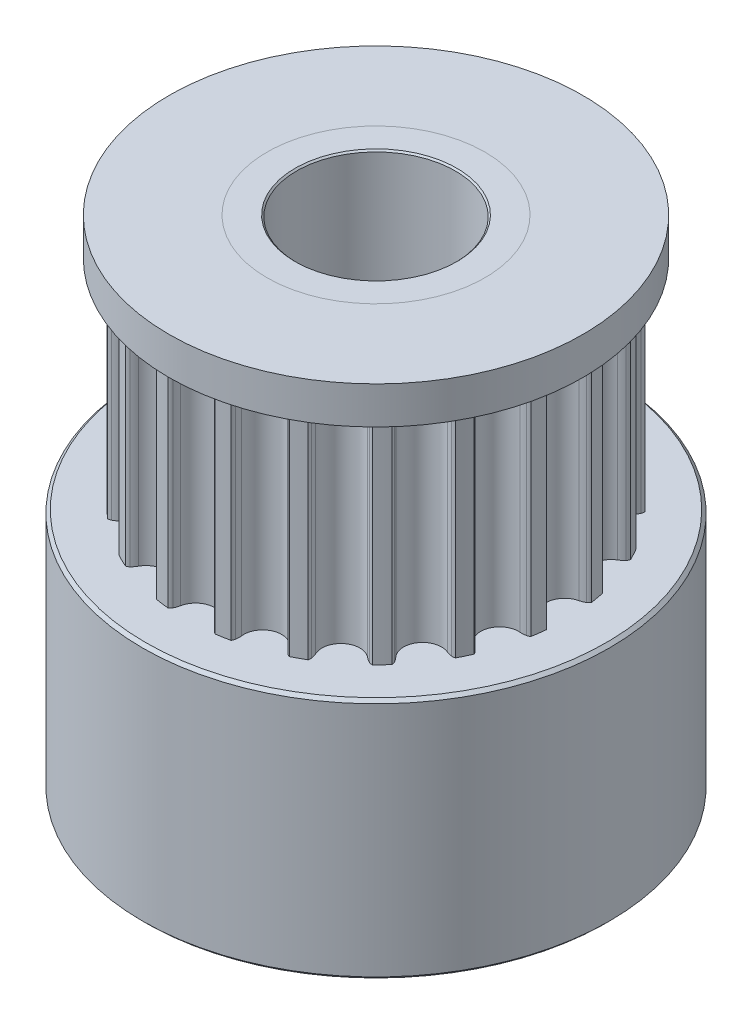
SolidWorks part; units mm, degrees
material "6061 slitina"
ref_plane "Přední rovina" through (0, 0, 0) normal (0, 0, 1) x (1, 0, 0)
ref_plane "Horní rovina" through (0, 0, 0) normal (0, 1, 0) x (1, 0, 0)
ref_plane "Pravá rovina" through (0, 0, 0) normal (1, 0, 0) x (0, 0, -1)
sketch "Skica1" plane through (0, 0, 0) normal (0, 1, 0) x (1, 0, 0)
  circle A0 centre (0, 0) radius 2.5
  arc B0 (-5.7301, 1.0983) -> (-5.3872, 2.2403) centre (-5.6803, 1.7058) ccw
  arc B1 (-5.7301, 1.0983) -> (-5.922, 1.0859) centre (-5.7841, 0.4401) ccw
  arc B2 (-5.922, 1.0859) -> (-6.0197, 1.0387) centre (-5.8743, 0.8624) ccw
  arc B3 (-6.0197, 1.0387) -> (-6.0791, 0.6004) centre (0, 0) ccw
  arc B4 (-6.0791, 0.6004) -> (-5.9974, 0.5289) centre (-5.892, 0.7317) ccw
  arc B5 (-5.9974, 0.5289) -> (-5.8158, 0.466) centre (-5.6927, 1.1148) ccw
  arc B6 (-5.7891, -0.7262) -> (-5.8158, 0.466) centre (-5.9294, -0.133) ccw
  arc B7 (-5.7891, -0.7262) -> (-5.9677, -0.7972) centre (-5.637, -1.3689) ccw
  arc B8 (-5.9677, -0.7972) -> (-6.0461, -0.8723) centre (-5.8532, -0.9951) ccw
  arc B9 (-6.0461, -0.8723) -> (-5.9671, -1.3075) centre (0, 0) ccw
  arc B10 (-5.9671, -1.3075) -> (-5.8673, -1.3503) centre (-5.8297, -1.1248) ccw
  arc B11 (-5.8673, -1.3503) -> (-5.6751, -1.354) centre (-5.7586, -0.6989) ccw
  arc B12 (-5.2813, -2.4796) -> (-5.6751, -1.354) centre (-5.5981, -1.9587) ccw
  arc B13 (-5.2813, -2.4796) -> (-5.4293, -2.6023) centre (-4.9381, -3.0438) ccw
  arc B14 (-5.4293, -2.6023) -> (-5.4806, -2.698) centre (-5.2593, -2.7551) ccw
  arc B15 (-5.4806, -2.698) -> (-5.271, -3.0875) centre (0, 0) ccw
  arc B16 (-5.271, -3.0875) -> (-5.1629, -3.0973) centre (-5.1968, -2.8713) ccw
  arc B17 (-5.1629, -3.0973) -> (-4.979, -3.0415) centre (-5.2608, -2.4442) ccw
  arc B18 (-4.2566, -3.9902) -> (-4.979, -3.0415) centre (-4.7188, -3.5928) ccw
  arc B19 (-4.2566, -3.9902) -> (-4.3594, -4.1527) centre (-3.7559, -4.4208) ccw
  arc B20 (-4.3594, -4.1527) -> (-4.3786, -4.2595) centre (-4.1505, -4.2455) ccw
  arc B21 (-4.3786, -4.2595) -> (-4.059, -4.5652) centre (0, 0) ccw
  arc B22 (-4.059, -4.5652) -> (-3.9531, -4.5412) centre (-4.0552, -4.3366) ccw
  arc B23 (-3.9531, -4.5412) -> (-3.7954, -4.4312) centre (-4.248, -3.9503) ccw
  arc B24 (-2.8152, -5.1103) -> (-3.7954, -4.4312) centre (-3.3776, -4.8751) ccw
  arc B25 (-2.8152, -5.1103) -> (-2.8628, -5.2965) centre (-2.2059, -5.3651) ccw
  arc B26 (-2.8628, -5.2965) -> (-2.8481, -5.4041) centre (-2.6354, -5.3203) ccw
  arc B27 (-2.8481, -5.4041) -> (-2.4496, -5.596) centre (0, 0) ccw
  arc B28 (-2.4496, -5.596) -> (-2.3563, -5.5405) centre (-2.5166, -5.3775) ccw
  arc B29 (-2.3563, -5.5405) -> (-2.2403, -5.3872) centre (-2.8194, -5.0696) ccw
  arc B30 (-1.0983, -5.7301) -> (-2.2403, -5.3872) centre (-1.7058, -5.6803) ccw
  arc B31 (-1.0983, -5.7301) -> (-1.0859, -5.922) centre (-0.4401, -5.7841) ccw
  arc B32 (-1.0859, -5.922) -> (-1.0387, -6.0197) centre (-0.8624, -5.8743) ccw
  arc B33 (-1.0387, -6.0197) -> (-0.6004, -6.0791) centre (0, 0) ccw
  arc B34 (-0.6004, -6.0791) -> (-0.5289, -5.9974) centre (-0.7317, -5.892) ccw
  arc B35 (-0.5289, -5.9974) -> (-0.466, -5.8158) centre (-1.1148, -5.6927) ccw
  arc B36 (0.7262, -5.7891) -> (-0.466, -5.8158) centre (0.133, -5.9294) ccw
  arc B37 (0.7262, -5.7891) -> (0.7972, -5.9677) centre (1.3689, -5.637) ccw
  arc B38 (0.7972, -5.9677) -> (0.8723, -6.0461) centre (0.9951, -5.8532) ccw
  arc B39 (0.8723, -6.0461) -> (1.3075, -5.9671) centre (0, 0) ccw
  arc B40 (1.3075, -5.9671) -> (1.3503, -5.8673) centre (1.1248, -5.8297) ccw
  arc B41 (1.3503, -5.8673) -> (1.354, -5.6751) centre (0.6989, -5.7586) ccw
  arc B42 (2.4796, -5.2813) -> (1.354, -5.6751) centre (1.9587, -5.5981) ccw
  arc B43 (2.4796, -5.2813) -> (2.6023, -5.4293) centre (3.0438, -4.9381) ccw
  arc B44 (2.6023, -5.4293) -> (2.698, -5.4806) centre (2.7551, -5.2593) ccw
  arc B45 (2.698, -5.4806) -> (3.0875, -5.271) centre (0, 0) ccw
  arc B46 (3.0875, -5.271) -> (3.0973, -5.1629) centre (2.8713, -5.1968) ccw
  arc B47 (3.0973, -5.1629) -> (3.0415, -4.979) centre (2.4442, -5.2608) ccw
  arc B48 (3.9902, -4.2566) -> (3.0415, -4.979) centre (3.5928, -4.7188) ccw
  arc B49 (3.9902, -4.2566) -> (4.1527, -4.3594) centre (4.4208, -3.7559) ccw
  arc B50 (4.1527, -4.3594) -> (4.2595, -4.3786) centre (4.2455, -4.1505) ccw
  arc B51 (4.2595, -4.3786) -> (4.5652, -4.059) centre (0, 0) ccw
  arc B52 (4.5652, -4.059) -> (4.5412, -3.9531) centre (4.3366, -4.0552) ccw
  arc B53 (4.5412, -3.9531) -> (4.4312, -3.7954) centre (3.9503, -4.248) ccw
  arc B54 (5.1103, -2.8152) -> (4.4312, -3.7954) centre (4.8751, -3.3776) ccw
  arc B55 (5.1103, -2.8152) -> (5.2965, -2.8628) centre (5.3651, -2.2059) ccw
  arc B56 (5.2965, -2.8628) -> (5.4041, -2.8481) centre (5.3203, -2.6354) ccw
  arc B57 (5.4041, -2.8481) -> (5.596, -2.4496) centre (0, 0) ccw
  arc B58 (5.596, -2.4496) -> (5.5405, -2.3563) centre (5.3775, -2.5166) ccw
  arc B59 (5.5405, -2.3563) -> (5.3872, -2.2403) centre (5.0696, -2.8194) ccw
  arc B60 (5.7301, -1.0983) -> (5.3872, -2.2403) centre (5.6803, -1.7058) ccw
  arc B61 (5.7301, -1.0983) -> (5.922, -1.0859) centre (5.7841, -0.4401) ccw
  arc B62 (5.922, -1.0859) -> (6.0197, -1.0387) centre (5.8743, -0.8624) ccw
  arc B63 (6.0197, -1.0387) -> (6.0791, -0.6004) centre (0, 0) ccw
  arc B64 (6.0791, -0.6004) -> (5.9974, -0.5289) centre (5.892, -0.7317) ccw
  arc B65 (5.9974, -0.5289) -> (5.8158, -0.466) centre (5.6927, -1.1148) ccw
  arc B66 (5.7891, 0.7262) -> (5.8158, -0.466) centre (5.9294, 0.133) ccw
  arc B67 (5.7891, 0.7262) -> (5.9677, 0.7972) centre (5.637, 1.3689) ccw
  arc B68 (5.9677, 0.7972) -> (6.0461, 0.8723) centre (5.8532, 0.9951) ccw
  arc B69 (6.0461, 0.8723) -> (5.9671, 1.3075) centre (0, 0) ccw
  arc B70 (5.9671, 1.3075) -> (5.8673, 1.3503) centre (5.8297, 1.1248) ccw
  arc B71 (5.8673, 1.3503) -> (5.6751, 1.354) centre (5.7586, 0.6989) ccw
  arc B72 (5.2813, 2.4796) -> (5.6751, 1.354) centre (5.5981, 1.9587) ccw
  arc B73 (5.2813, 2.4796) -> (5.4293, 2.6023) centre (4.9381, 3.0438) ccw
  arc B74 (5.4293, 2.6023) -> (5.4806, 2.698) centre (5.2593, 2.7551) ccw
  arc B75 (5.4806, 2.698) -> (5.271, 3.0875) centre (0, 0) ccw
  arc B76 (5.271, 3.0875) -> (5.1629, 3.0973) centre (5.1968, 2.8713) ccw
  arc B77 (5.1629, 3.0973) -> (4.979, 3.0415) centre (5.2608, 2.4442) ccw
  arc B78 (4.2566, 3.9902) -> (4.979, 3.0415) centre (4.7188, 3.5928) ccw
  arc B79 (4.2566, 3.9902) -> (4.3594, 4.1527) centre (3.7559, 4.4208) ccw
  arc B80 (4.3594, 4.1527) -> (4.3786, 4.2595) centre (4.1505, 4.2455) ccw
  arc B81 (4.3786, 4.2595) -> (4.059, 4.5652) centre (0, 0) ccw
  arc B82 (4.059, 4.5652) -> (3.9531, 4.5412) centre (4.0552, 4.3366) ccw
  arc B83 (3.9531, 4.5412) -> (3.7954, 4.4312) centre (4.248, 3.9503) ccw
  arc B84 (2.8152, 5.1103) -> (3.7954, 4.4312) centre (3.3776, 4.8751) ccw
  arc B85 (2.8152, 5.1103) -> (2.8628, 5.2965) centre (2.2059, 5.3651) ccw
  arc B86 (2.8628, 5.2965) -> (2.8481, 5.4041) centre (2.6354, 5.3203) ccw
  arc B87 (2.8481, 5.4041) -> (2.4496, 5.596) centre (0, 0) ccw
  arc B88 (2.4496, 5.596) -> (2.3563, 5.5405) centre (2.5166, 5.3775) ccw
  arc B89 (2.3563, 5.5405) -> (2.2403, 5.3872) centre (2.8194, 5.0696) ccw
  arc B90 (1.0983, 5.7301) -> (2.2403, 5.3872) centre (1.7058, 5.6803) ccw
  arc B91 (1.0983, 5.7301) -> (1.0859, 5.922) centre (0.4401, 5.7841) ccw
  arc B92 (1.0859, 5.922) -> (1.0387, 6.0197) centre (0.8624, 5.8743) ccw
  arc B93 (1.0387, 6.0197) -> (0.6004, 6.0791) centre (0, 0) ccw
  arc B94 (0.6004, 6.0791) -> (0.5289, 5.9974) centre (0.7317, 5.892) ccw
  arc B95 (0.5289, 5.9974) -> (0.466, 5.8158) centre (1.1148, 5.6927) ccw
  arc B96 (-0.7262, 5.7891) -> (0.466, 5.8158) centre (-0.133, 5.9294) ccw
  arc B97 (-0.7262, 5.7891) -> (-0.7972, 5.9677) centre (-1.3689, 5.637) ccw
  arc B98 (-0.7972, 5.9677) -> (-0.8723, 6.0461) centre (-0.9951, 5.8532) ccw
  arc B99 (-0.8723, 6.0461) -> (-1.3075, 5.9671) centre (0, 0) ccw
  arc B100 (-1.3075, 5.9671) -> (-1.3503, 5.8673) centre (-1.1248, 5.8297) ccw
  arc B101 (-1.3503, 5.8673) -> (-1.354, 5.6751) centre (-0.6989, 5.7586) ccw
  arc B102 (-2.4796, 5.2813) -> (-1.354, 5.6751) centre (-1.9587, 5.5981) ccw
  arc B103 (-2.4796, 5.2813) -> (-2.6023, 5.4293) centre (-3.0438, 4.9381) ccw
  arc B104 (-2.6023, 5.4293) -> (-2.698, 5.4806) centre (-2.7551, 5.2593) ccw
  arc B105 (-2.698, 5.4806) -> (-3.0875, 5.271) centre (0, 0) ccw
  arc B106 (-3.0875, 5.271) -> (-3.0973, 5.1629) centre (-2.8713, 5.1968) ccw
  arc B107 (-3.0973, 5.1629) -> (-3.0415, 4.979) centre (-2.4442, 5.2608) ccw
  arc B108 (-3.9902, 4.2566) -> (-3.0415, 4.979) centre (-3.5928, 4.7188) ccw
  arc B109 (-3.9902, 4.2566) -> (-4.1527, 4.3594) centre (-4.4208, 3.7559) ccw
  arc B110 (-4.1527, 4.3594) -> (-4.2595, 4.3786) centre (-4.2455, 4.1505) ccw
  arc B111 (-4.2595, 4.3786) -> (-4.5652, 4.059) centre (0, 0) ccw
  arc B112 (-4.5652, 4.059) -> (-4.5412, 3.9531) centre (-4.3366, 4.0552) ccw
  arc B113 (-4.5412, 3.9531) -> (-4.4312, 3.7954) centre (-3.9503, 4.248) ccw
  arc B114 (-5.1103, 2.8152) -> (-4.4312, 3.7954) centre (-4.8751, 3.3776) ccw
  arc B115 (-5.1103, 2.8152) -> (-5.2965, 2.8628) centre (-5.3651, 2.2059) ccw
  arc B116 (-5.2965, 2.8628) -> (-5.4041, 2.8481) centre (-5.3203, 2.6354) ccw
  arc B117 (-5.4041, 2.8481) -> (-5.596, 2.4496) centre (0, 0) ccw
  arc B118 (-5.596, 2.4496) -> (-5.5405, 2.3563) centre (-5.3775, 2.5166) ccw
  arc B119 (-5.5405, 2.3563) -> (-5.3872, 2.2403) centre (-5.0696, 2.8194) ccw
  dimension "D1" = 5
sketch_block_instance "Blok1-1"
sketch_block "Blok1"
extrude "Přidat vysunutím1" add sketch "Skica1" along normal blind 7 from offset 7.8
sketch "Skica2" plane through (0, 7.8, 0) normal (0, -1, 0) x (1, 0, 0)
  circle A0 centre (0, 0) radius 3.5
  circle A1 centre (0, 0) radius 2.5 construction
  circle A2 centre (0, 0) radius 2.5
  dimension "D1" = 7
extrude "Přidat vysunutím2" add sketch "Skica2" along normal blind 7.8
sketch "Skica3" plane through (0, 14.8, 0) normal (0, 1, 0) x (1, 0, 0)
  circle A0 centre (0, 0) radius 3.5
  circle A1 centre (0, 0) radius 2.5 construction
  circle A2 centre (0, 0) radius 2.5
  dimension "D1" = 7
extrude "Přidat vysunutím3" add sketch "Skica3" along normal blind 1.2
sketch "Skica5" plane through (0, 16, 0) normal (0, 1, 0) x (1, 0, 0)
  circle A0 centre (0, 0) radius 7.5
  circle A3 centre (0, 0) radius 3.5 construction
  circle A4 centre (0, 0) radius 3.5
  dimension "D1" = 15
extrude "Přidat vysunutím4" add sketch "Skica5" against normal up to surface (1.2 mm away) separate body up to face at (0, 14.8, 0)
sketch "Skica6" plane through (0, 0, 0) normal (0, -1, 0) x (1, 0, 0)
  circle A0 centre (0, 0) radius 7.5
  circle A1 centre (0, 0) radius 3.5 construction
  circle A2 centre (0, 0) radius 3.5
  circle A3 centre (0, 0) radius 7.5 construction
extrude "Přidat vysunutím5" add sketch "Skica6" against normal up to surface (7.8 mm away) separate body up to face at (0, 7.8, 0)
chamfer "Zkosení1" distance 0.1 angle 45 2 edges at (0, 14.8, 7.5) (0, 16, 7.5)
chamfer "Zkosení2" distance 0.1 angle 45 2 edges at (0, 0, -2.5) (0, 16, 2.5)
chamfer "Zkosení3" distance 0.1 angle 45 2 edges at (0, 0, -7.5) (0, 7.8, 7.5)
sketch "Sketch7" plane through (0, 0, 0) normal (0, -1, 0) x (1, 0, 0)
  circle A1 centre (0, 0) radius 4.05
  dimension "D1" = 8.1
sketch "Sketch8" plane through (0, 16, 0) normal (0, 1, 0) x (1, 0, 0)
  circle A0 centre (0, 0) radius 6.65
extrude "Cut-Extrude2" cut sketch "Sketch8" against normal blind 5 flip side to cut contours A0
ref_plane "Plane1" through (0, 0, -7.5) normal (0, 0, -1) x (-1, 0, 0)
ref_plane "Plane2" through (-7.5, 0, 0) normal (-1, 0, 0) x (0, 0, 1)
sketch "Sketch19" plane through (0, 0, -7.5) normal (0, 0, -1) x (-1, 0, 0)
  line L0 (0, 0.1) -> (0, 7.7)
  line L1 (7.5, 0.1) -> (-7.5, 0.1) construction
  line L2 (7.5, 7.7) -> (-7.5, 7.7) construction
  circle A0 centre (0, 3.9) radius 1.5
extrude "Cut-Extrude6" cut sketch "Sketch19" against normal blind 8 contours A0
sketch "Sketch20" plane through (-7.5, 0, 0) normal (-1, 0, 0) x (0, 0, 1)
  line L0 (0, 0.1) -> (0, 7.7)
  line L1 (-7.5, 0.1) -> (7.5, 0.1) construction
  line L2 (7.5, 7.7) -> (-7.5, 7.7) construction
  circle A0 centre (0, 3.9) radius 1.5
extrude "Cut-Extrude7" cut sketch "Sketch20" against normal blind 8 contours A0
sketch "Sketch21" plane through (0, 16, 0) normal (0, 1, 0) x (1, 0, 0)
  circle A0 centre (0, 0) radius 2.55
extrude "Cut-Extrude8" cut sketch "Sketch21" against normal blind 30
